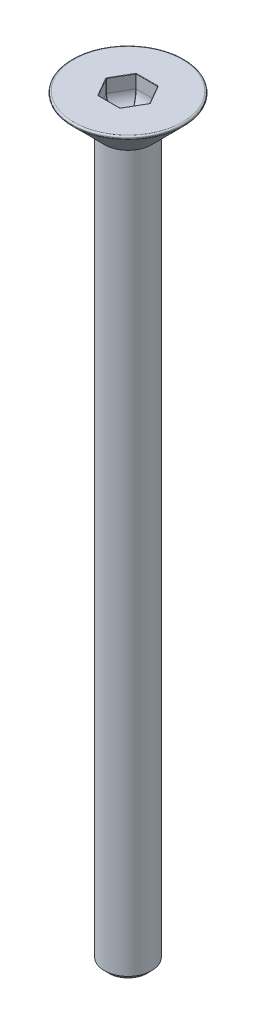
SolidWorks part; units mm, degrees
ref_plane "Front" through (0, 0, 0) normal (0, 0, 1) x (1, 0, 0)
ref_plane "Top" through (0, 0, 0) normal (0, 1, 0) x (1, 0, 0)
ref_plane "Right" through (0, 0, 0) normal (1, 0, 0) x (0, 0, -1)
sketch "Sketch8" plane through (0, 0, 0) normal (0, 0, 1) x (1, 0, 0)
  line L1 (0, 0) -> (1.25, 0)
  line L2 (0, 0) -> (0, -40)
  line L3 (0, -40) -> (1.25, -40)
  line L4 (1.25, 0) -> (1.25, -40)
  dimension "D1" = 40
revolve "Revolve1" add sketch "Sketch8" angle 360 about L2
chamfer "Chamfer1" distance 0.25 angle 45 1 edges at (-1.25, -40, 0)
sketch "Sketch9" plane through (0, 0, 0) normal (0, 1, 0) x (1, 0, 0)
  circle A0 centre (0, 0) radius 1.5
thread "Thread2" pitch 0.5 start angle 0, offset 0, length 15, pitch 0.5, diameter 3
ref_plane "Plane2" through (-1.5, 0, 0) normal (0, 0, -1) x (1, 0, 0)
sketch "Thread Profile2" plane through (-1.5, 0, 0) normal (0, 0, -1) x (1, 0, 0)
  line L0 (0, 0) -> (0, 0.5) construction
  line L11 (0, 0.4375) -> (0, 0)
  line L12 (0, 0) -> (0.2706, 0.1563)
  line L13 (0.2706, 0.1563) -> (0.2706, 0.2813)
  line L15 (0.2706, 0.2813) -> (0, 0.4375)
  line L17 (0.2706, 0.2188) -> (0, 0.2188) construction
  point P3 (0, 0)
  dimension "Pitch" = 0.5
  dimension "Profile_Angle" = 60
  dimension "Profile_Land" = 0.125
  dimension "Profile_Height" = 0.2706
sketch "Sketch13" plane through (0, 0, 0) normal (0, 0, 1) x (1, 0, 0)
  line L0 (0, 0) -> (3.1, 0)
  line L1 (0, 0) -> (0, -3.1)
  line L2 (0, -3.1) -> (3.1, 0)
  line L3 (1.55, 0) -> (1.55, -1.55) construction
revolve "Revolve2" add sketch "Sketch13" angle 360 about L1
chamfer "Chamfer2" distance 0.2 angle 45 1 edges at (-3.1, 0, 0)
fillet "Fillet1" radius 0.08 2 edges at (2.9586, 0, 0) (2.9586, -0.1414, 0)
sketch "Sketch14" plane through (0, 0, 0) normal (0, 1, 0) x (1, 0, 0)
  line L1 (1.1547, 0) -> (0.5774, 1)
  line L2 (0.5774, 1) -> (-0.5774, 1)
  line L3 (-0.5774, 1) -> (-1.1547, 0)
  line L4 (-1.1547, 0) -> (-0.5774, -1)
  line L5 (-0.5774, -1) -> (0.5774, -1)
  line L6 (0.5774, -1) -> (1.1547, 0)
  circle A0 centre (0, 0) radius 1 construction
extrude "Cut-Extrude1" cut sketch "Sketch14" against normal blind 1.5
fillet "Fillet2" radius 0.8 6 edges at (0, -1.5, 1) (-0.866, -1.5, 0.5) (-0.866, -1.5, -0.5) (0, -1.5, -1) (0.866, -1.5, -0.5) (0.866, -1.5, 0.5)
fillet "Fillet5" radius 0.02 18 edges at (0, 0, -1) (-0.866, 0, -0.5) (-0.866, 0, 0.5) (0, 0, 1) (0.866, 0, 0.5) (0.866, 0, -0.5) (-0.8841, -1.2657, 0) (-0.4421, -1.2657, 0.7657) (0.4421, -1.2657, 0.7657) (0.8841, -1.2657, 0) (0.4421, -1.2657, -0.7657) (-0.4421, -1.2657, -0.7657) (-1.1547, -0.35, 0) (-0.5774, -0.35, 1) (0.5774, -0.35, 1) (1.1547, -0.35, 0) (0.5774, -0.35, -1) (-0.5774, -0.35, -1)
equation "\"length\"= 8"
